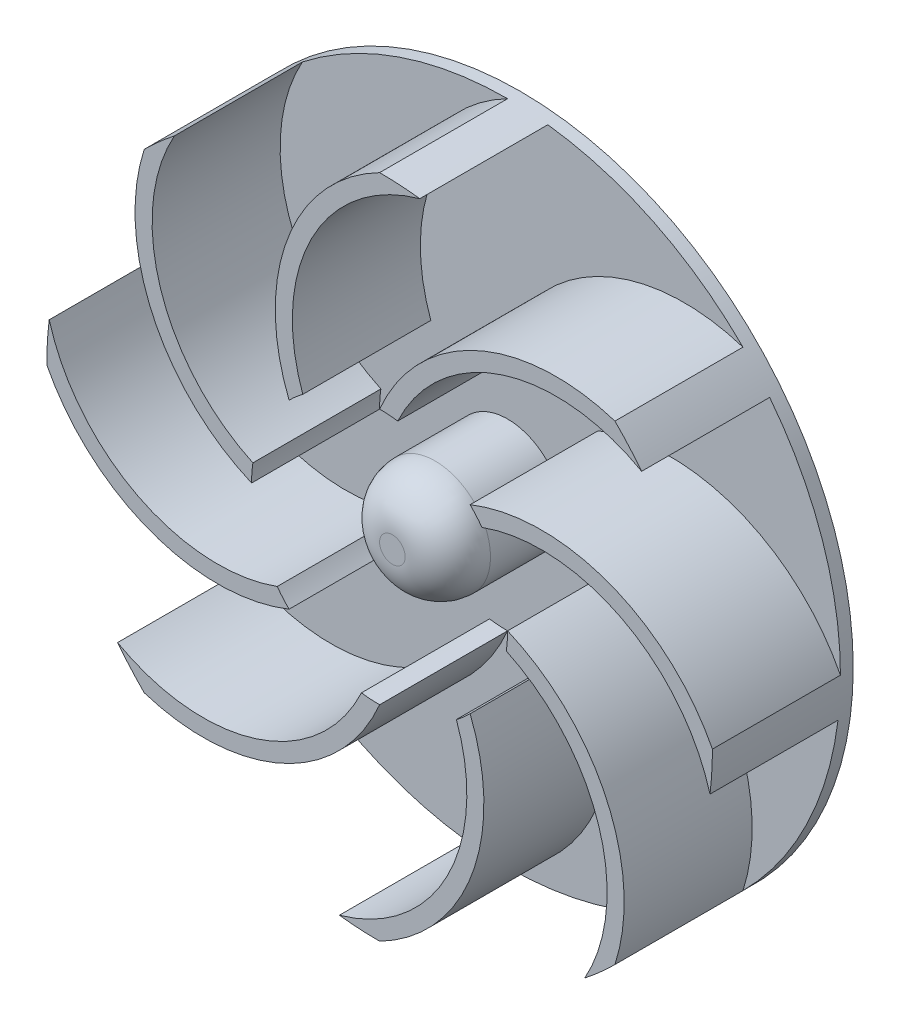
SolidWorks part; units mm, degrees
ref_plane "Front Plane" through (0, 0, 0) normal (0, 0, 1) x (1, 0, 0)
ref_plane "Top Plane" through (0, 0, 0) normal (0, 1, 0) x (1, 0, 0)
ref_plane "Right Plane" through (0, 0, 0) normal (1, 0, 0) x (0, 0, -1)
sketch "Sketch1" plane through (0, 0, 0) normal (1, 0, 0) x (0, 0, -1)
  line L6 (0, 0) -> (0, 26)
  line L7 (0, 26) -> (-1, 26)
  line L8 (-1, 26) -> (-1, 4.3333)
  line L9 (-1, 4.3333) -> (-6.6667, 4.3333)
  line L10 (-10, 1) -> (-10, 0)
  line L11 (-10, 0) -> (0, 0)
  arc A1 (-6.6667, 4.3333) -> (-10, 1) centre (-6.6667, 1) ccw
  point P9 (-10, 4.3333)
  dimension "D5" = 3.3333
  dimension "D1" = 1
  dimension "D2" = 26
  dimension "D3" = 10
  dimension "D4" = 4.3333
revolve "Revolve2" add sketch "Sketch1" angle 360 about L11
sketch "Sketch3" plane through (0, 0, 1) normal (0, 0, 1) x (1, 0, 0)
  line L0 (0, 0) -> (0, 26) construction
  line L1 (0, 0) -> (-7.0711, 7.0711) construction
  arc A0 (-5.9989, 8.0008) -> (-7.0711, 7.0711) centre (0, 0) ccw
  circle A1 centre (0, 0) radius 26 construction
  arc A2 (-7.0711, 7.0711) -> (0, 26) centre (6.8506, 12.6557) cw
  arc A3 (-5.9989, 8.0008) -> (3.1417, 25.8095) centre (6.8506, 12.6557) cw
  arc A4 (3.1417, 25.8095) -> (0, 26) centre (0, 0) ccw
  arc A5 (-5.8336, 7.5675) -> (0.6089, 24.8138) centre (6.8506, 12.6557) cw construction
  dimension "D1" = 20
  dimension "D3" = 15
  dimension "D2" = 45
  dimension "D4" = 1.3333
extrude "Boss-Extrude1" add sketch "Sketch3" along normal blind 10
pattern_circular "CirPattern1" count 8 over 360 about axis through (0, 0, 0) along (0, 0, 1) of "Boss-Extrude1"
sketch "Sketch4" plane through (0, 0, 0) normal (0, 0, -1) x (-1, 0, 0)
  circle A0 centre (0, 0) radius 2.5
  dimension "D1" = 5
extrude "Boss-Extrude2" add sketch "Sketch4" along normal blind 11.8333
sketch "Sketch5" plane through (0, 0, -11.8333) normal (0, 0, -1) x (-1, 0, 0)
  circle A0 centre (0, 0) radius 1.5
  dimension "D1" = 3
extrude "Cut-Extrude1" cut sketch "Sketch5" against normal blind 10
